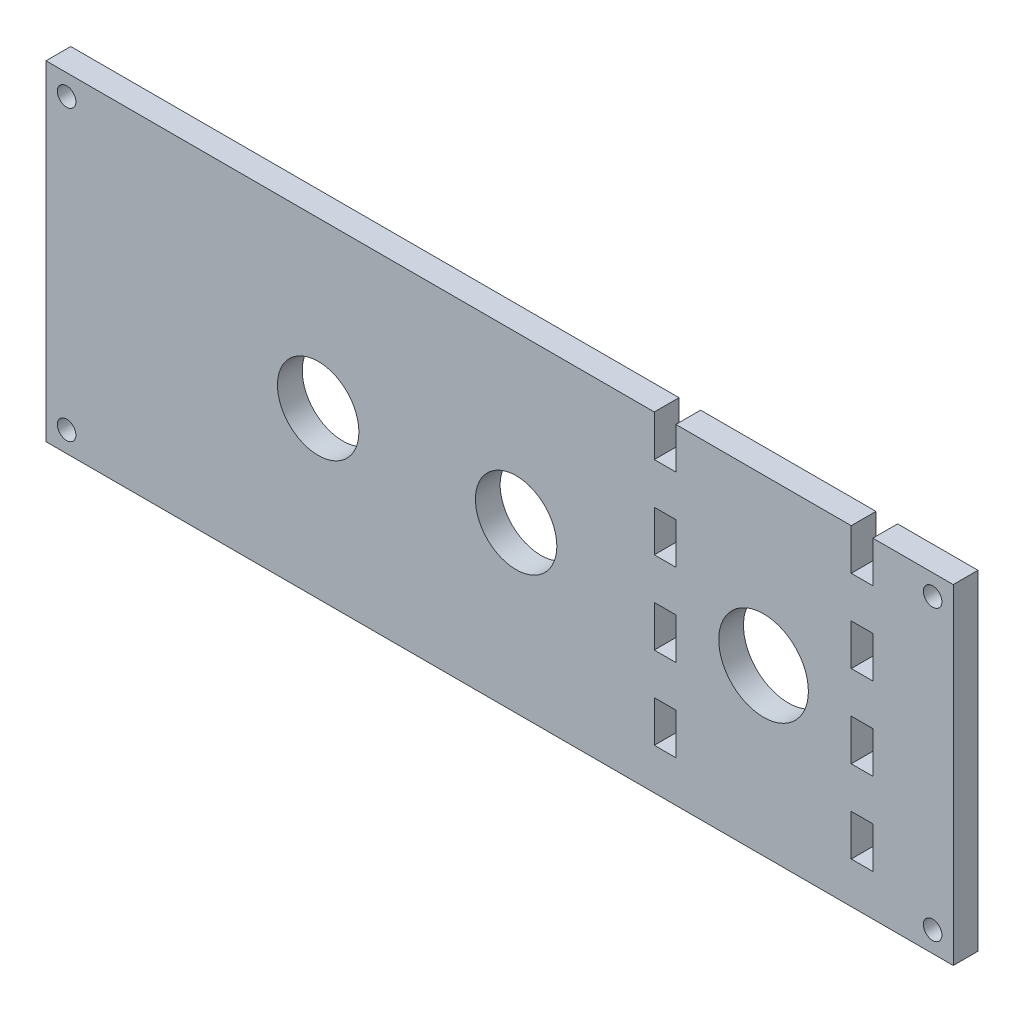
SolidWorks part; units mm, degrees
ref_plane "Front Plane" through (0, 0, 0) normal (0, 0, 1) x (1, 0, 0)
ref_plane "Top Plane" through (0, 0, 0) normal (0, 1, 0) x (1, 0, 0)
ref_plane "Right Plane" through (0, 0, 0) normal (1, 0, 0) x (0, 0, -1)
sketch "Sketch1" plane through (0, 0, 0) normal (0, 0, 1) x (1, 0, 0)
  line L1 (0, 0) -> (110, 0)
  line L2 (0, 0) -> (0, 40)
  line L3 (0, 40) -> (110, 40)
  line L4 (110, 0) -> (110, 40)
  dimension "D1" = 110
  dimension "D2" = 40
extrude "Boss-Extrude1" add sketch "Sketch1" along normal blind 3 contours L3 L4 L1 L2
sketch "Sketch2" plane through (0, 0, 3) normal (0, 0, 1) x (1, 0, 0)
  line L0 (0, 20) -> (110, 20) construction
  line L1 (0, 0) -> (0, 40) construction
  line L2 (110, 0) -> (110, 40) construction
  line L3 (0, 40) -> (110, 40) construction
  line L4 (55, 40) -> (55, 0) construction
  line L5 (0, 0) -> (110, 0) construction
  line L6 (48.175, 16) -> (48.175, 8)
  line L7 (45, 32) -> (48.175, 32)
  line L8 (45, 32) -> (45, 24)
  line L9 (45, 24) -> (48.175, 24)
  line L10 (48.175, 32) -> (48.175, 24)
  line L11 (45, 8) -> (48.175, 8)
  line L12 (45, 16) -> (45, 8)
  line L13 (45, 16) -> (48.175, 16)
  line L14 (48.175, 32) -> (48.175, 16) construction
  line L15 (0, 40) -> (110, 40) construction
  line L16 (97.63, 40) -> (100.25, 40)
  line L17 (97.63, 40) -> (97.63, 35)
  line L18 (97.63, 35) -> (100.25, 35)
  line L19 (100.25, 40) -> (100.25, 35)
  line L20 (73.75, 35) -> (76.37, 35)
  line L21 (76.37, 40) -> (76.37, 35)
  line L22 (73.75, 40) -> (73.75, 35)
  line L23 (73.75, 40) -> (76.37, 40)
  line L24 (73.75, 25) -> (76.37, 25)
  line L25 (76.37, 30) -> (76.37, 25)
  line L26 (73.75, 30) -> (73.75, 25)
  line L27 (73.75, 30) -> (76.37, 30)
  line L28 (73.75, 15) -> (76.37, 15)
  line L29 (76.37, 20) -> (76.37, 15)
  line L30 (73.75, 20) -> (73.75, 15)
  line L31 (73.75, 20) -> (76.37, 20)
  line L32 (73.75, 5) -> (76.37, 5)
  line L33 (76.37, 10) -> (76.37, 5)
  line L34 (73.75, 10) -> (73.75, 5)
  line L35 (73.75, 10) -> (76.37, 10)
  line L36 (97.63, 25) -> (100.25, 25)
  line L37 (100.25, 30) -> (100.25, 25)
  line L38 (97.63, 30) -> (97.63, 25)
  line L39 (97.63, 30) -> (100.25, 30)
  line L40 (97.63, 15) -> (100.25, 15)
  line L41 (100.25, 20) -> (100.25, 15)
  line L42 (97.63, 20) -> (97.63, 15)
  line L43 (97.63, 20) -> (100.25, 20)
  line L44 (97.63, 5) -> (100.25, 5)
  line L45 (100.25, 10) -> (100.25, 5)
  line L46 (97.63, 10) -> (97.63, 5)
  line L47 (97.63, 10) -> (100.25, 10)
  line L48 (97.63, 35) -> (73.75, 35) construction
  line L49 (73.75, 40) -> (100.25, 40) construction
  circle A1 centre (33, 20) radius 4.9365
  circle A2 centre (57, 20) radius 4.9365
  circle A3 centre (2.5, 37.5) radius 1.125
  circle A4 centre (107.5, 37.5) radius 1.125
  circle A5 centre (107.5, 2.5) radius 1.125
  circle A6 centre (2.5, 2.5) radius 1.125
  circle A7 centre (87, 20) radius 5.435
  point P42 (87, 40)
  dimension "D1" = 33
  dimension "D2" = 9.873
  dimension "D3" = 9.873
  dimension "D7" = 2.25
  dimension "D15" = 10.87
  dimension "D4" = 3.175
  dimension "D5" = 8
  dimension "D6" = 24
  dimension "D8" = 2.5
  dimension "D9" = 2.5
  dimension "D10" = 12
  dimension "D11" = 16
  dimension "D13" = 16
  dimension "D14" = 30
  dimension "D16" = 2.62
  dimension "D17" = 5
  dimension "D18" = 26.5
  dimension "D22" = 10
  dimension "D12" = 2
  dimension "D19" = 2
  dimension "D20" = 4
extrude "Cut-Extrude1" cut sketch "Sketch2" against normal through all
